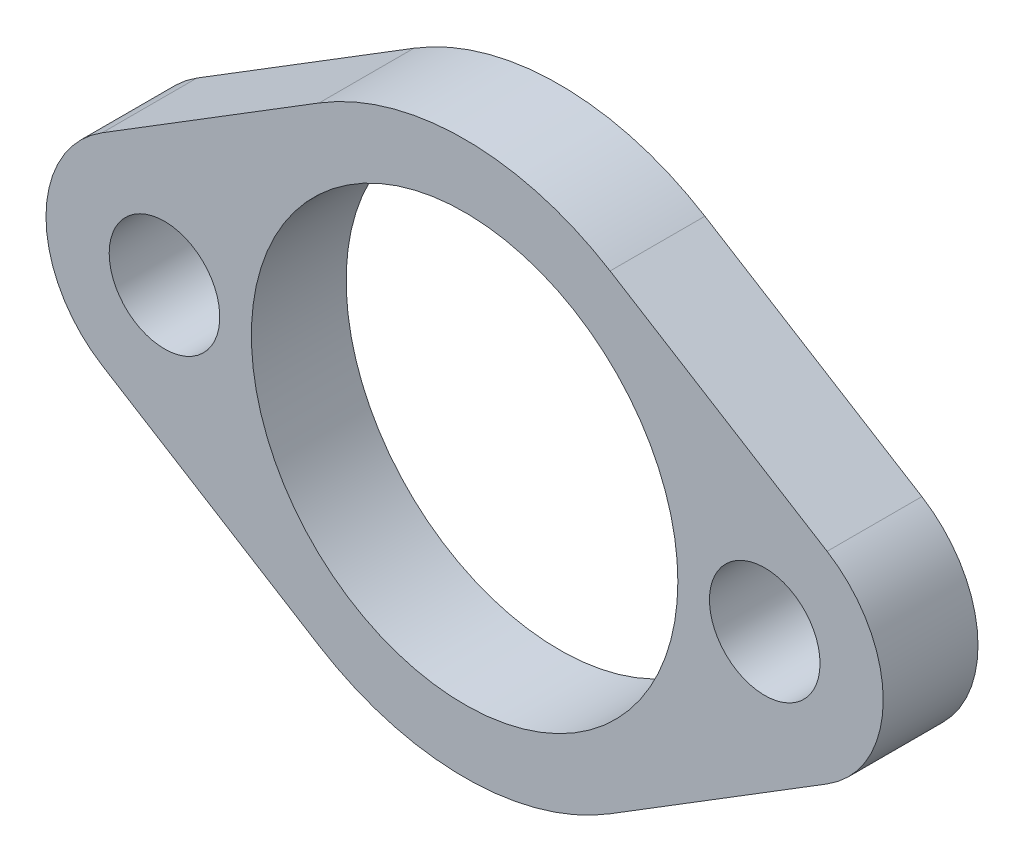
SolidWorks part; units mm, degrees
ref_plane "Płaszczyzna przednia" through (0, 0, 0) normal (0, 0, 1) x (1, 0, 0)
ref_plane "Płaszczyzna górna" through (0, 0, 0) normal (0, 1, 0) x (1, 0, 0)
ref_plane "Płaszczyzna prawa" through (0, 0, 0) normal (1, 0, 0) x (0, 0, -1)
sketch "Szkic1" plane through (0, 0, 0) normal (0, 0, 1) x (1, 0, 0)
  line L0 (0, 16.9057) -> (0, -20.0352) construction
  line L1 (3.5526, 5.7395) -> (10.4211, 1.488) construction
  line L2 (3.5526, -5.7395) -> (10.4211, -1.488) construction
  line L3 (-17.5655, 0) -> (23.1095, 0) construction
  line L4 (4.6053, 7.44) -> (11.4737, 3.1886)
  line L5 (4.6053, -7.44) -> (11.4737, -3.1886)
  line L8 (-4.6053, 7.44) -> (-11.4737, 3.1886)
  line L9 (-4.6053, -7.44) -> (-11.4737, -3.1886)
  circle A0 centre (0, 0) radius 6.75
  circle A1 centre (9.5, 0) radius 1.75
  arc A2 (11.4737, 3.1886) -> (11.4737, -3.1886) centre (9.5, 0) cw
  arc A3 (4.6053, 7.44) -> (-4.6053, 7.44) centre (0, 0) ccw
  arc A4 (4.6053, -7.44) -> (-4.6053, -7.44) centre (0, 0) cw
  circle A5 centre (-9.5, 0) radius 1.75
  arc A6 (-11.4737, 3.1886) -> (-11.4737, -3.1886) centre (-9.5, 0) ccw
  dimension "D1" = 13.5
  dimension "D2" = 3.5
  dimension "D3" = 19
  dimension "D4" = 2
extrude "Dodanie-wyciągnięcie1" add sketch "Szkic1" along normal blind 3
